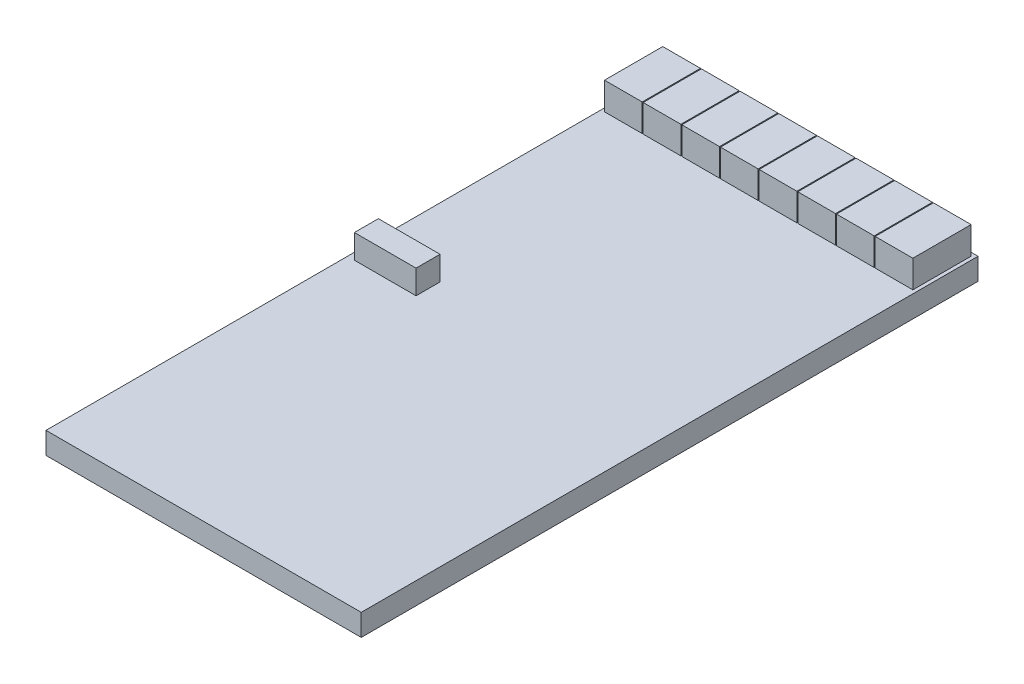
SolidWorks part; units mm, degrees
ref_plane "Front Plane" through (0, 0, 0) normal (0, 0, 1) x (1, 0, 0)
ref_plane "Top Plane" through (0, 0, 0) normal (0, 1, 0) x (1, 0, 0)
ref_plane "Right Plane" through (0, 0, 0) normal (1, 0, 0) x (0, 0, -1)
sketch "Sketch1" plane through (0, 0, 0) normal (0, 1, 0) x (1, 0, 0)
  line L1 (0, 0) -> (23, 0)
  line L2 (0, 0) -> (0, 45)
  line L3 (0, 45) -> (23, 45)
  line L4 (23, 0) -> (23, 45)
extrude "Boss-Extrude1" add sketch "Sketch1" along normal blind 1.5875
sketch "Sketch2" plane through (0, 0, 0) normal (0, -1, 0) x (1, 0, 0)
  line L1 (3.25, -8.25) -> (19.75, -8.25)
  line L2 (3.25, -8.25) -> (3.25, -24.75)
  line L3 (3.25, -24.75) -> (19.75, -24.75)
  line L4 (19.75, -8.25) -> (19.75, -24.75)
extrude "Boss-Extrude2" add sketch "Sketch2" along normal blind 1.14 draft 42.37
sketch "Sketch3" plane through (0, -1.14, 0) normal (0, -1, 0) x (1, 0, 0)
  line L1 (4.29, -9.29) -> (18.71, -9.29)
  line L2 (4.29, -9.29) -> (4.29, -23.71)
  line L3 (4.29, -23.71) -> (18.71, -23.71)
  line L4 (18.71, -9.29) -> (18.71, -23.71)
extrude "Boss-Extrude3" add sketch "Sketch3" along normal blind 0.26
sketch "Sketch4" plane through (0, 1.5875, 0) normal (0, 1, 0) x (1, 0, 0)
  line L0 (3.071, 40.5) -> (5.821, 40.5)
  line L1 (0.25, 40.5) -> (3, 40.5)
  line L2 (0.25, 40.5) -> (0.25, 44.75)
  line L3 (0.25, 44.75) -> (3, 44.75)
  line L4 (3, 40.5) -> (3, 44.75)
  line L5 (3.071, 40.5) -> (3.071, 44.75)
  line L6 (3.071, 44.75) -> (5.821, 44.75)
  line L7 (5.821, 40.5) -> (5.821, 44.75)
  line L8 (5.892, 40.5) -> (8.642, 40.5)
  line L9 (5.892, 40.5) -> (5.892, 44.75)
  line L10 (5.892, 44.75) -> (8.642, 44.75)
  line L11 (8.642, 40.5) -> (8.642, 44.75)
  line L12 (8.713, 40.5) -> (11.463, 40.5)
  line L13 (8.713, 40.5) -> (8.713, 44.75)
  line L14 (8.713, 44.75) -> (11.463, 44.75)
  line L15 (11.463, 40.5) -> (11.463, 44.75)
  line L16 (11.534, 40.5) -> (14.284, 40.5)
  line L17 (11.534, 40.5) -> (11.534, 44.75)
  line L18 (11.534, 44.75) -> (14.284, 44.75)
  line L19 (14.284, 40.5) -> (14.284, 44.75)
  line L20 (14.355, 40.5) -> (17.105, 40.5)
  line L21 (14.355, 40.5) -> (14.355, 44.75)
  line L22 (14.355, 44.75) -> (17.105, 44.75)
  line L23 (17.105, 40.5) -> (17.105, 44.75)
  line L24 (17.176, 40.5) -> (19.926, 40.5)
  line L25 (17.176, 40.5) -> (17.176, 44.75)
  line L26 (17.176, 44.75) -> (19.926, 44.75)
  line L27 (19.926, 40.5) -> (19.926, 44.75)
  line L28 (19.997, 40.5) -> (22.747, 40.5)
  line L29 (19.997, 40.5) -> (19.997, 44.75)
  line L30 (19.997, 44.75) -> (22.747, 44.75)
  line L31 (22.747, 40.5) -> (22.747, 44.75)
  dimension "D1" = 8
extrude "Boss-Extrude4" add sketch "Sketch4" along normal blind 2
sketch "Sketch5" plane through (0, 1.5875, 0) normal (0, 1, 0) x (1, 0, 0)
  line L1 (0.5, 22) -> (5, 22)
  line L2 (0.5, 22) -> (0.5, 23.75)
  line L3 (0.5, 23.75) -> (5, 23.75)
  line L4 (5, 22) -> (5, 23.75)
extrude "Boss-Extrude5" add sketch "Sketch5" along normal blind 1.75
